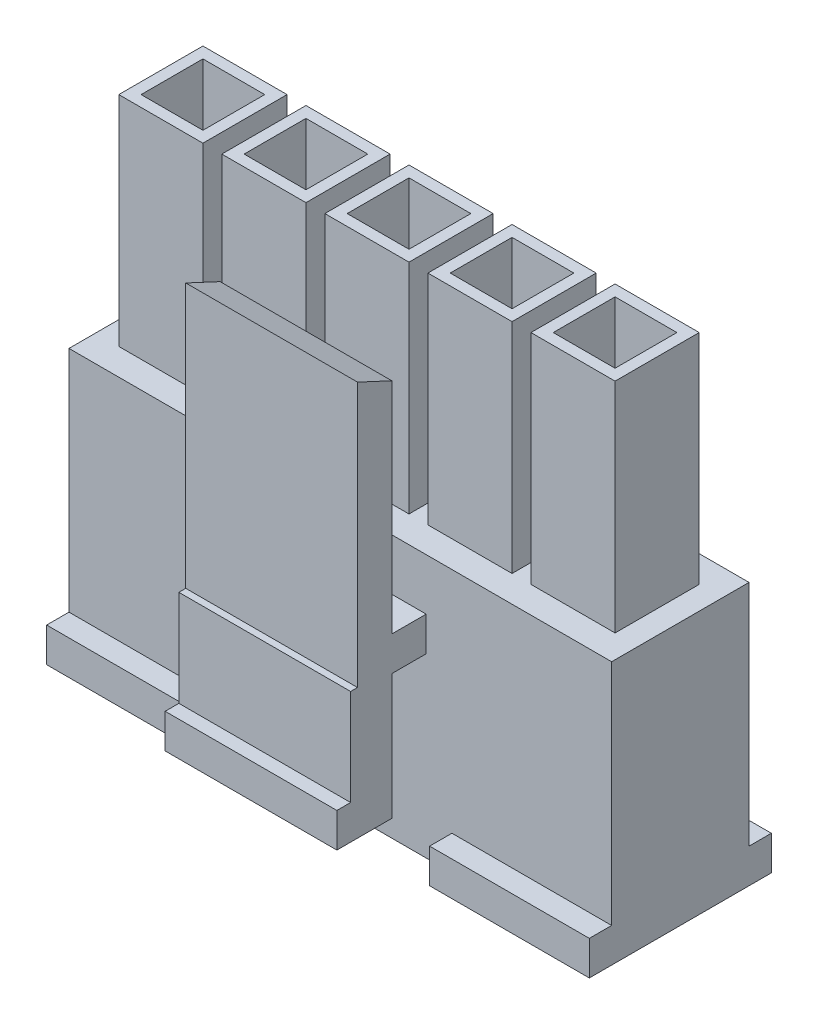
SolidWorks part; units mm, degrees
ref_plane "Front Plane" through (0, 0, 0) normal (0, 0, 1) x (1, 0, 0)
ref_plane "Top Plane" through (0, 0, 0) normal (0, 1, 0) x (1, 0, 0)
ref_plane "Right Plane" through (0, 0, 0) normal (1, 0, 0) x (0, 0, -1)
sketch "Sketch1" plane through (0, 0, 0) normal (0, 1, 0) x (1, 0, 0)
  line L0 (0, 2) -> (0, -2) construction
  line L1 (-7.9, 2) -> (7.9, 2)
  line L2 (-7.9, 2) -> (-7.9, -2)
  line L3 (-7.9, -2) -> (7.9, -2)
  line L4 (7.9, 2) -> (7.9, -2)
  line L5 (-7.9, 2) -> (7.9, -2) construction
  line L6 (-7.9, -2) -> (7.9, 2) construction
  line L7 (-1.35, 1.35) -> (1.35, 1.35)
  line L8 (-1.35, 1.35) -> (-1.35, -1.35)
  line L9 (-1.35, -1.35) -> (1.35, -1.35)
  line L10 (1.35, 1.35) -> (1.35, -1.35)
  line L11 (-1.35, 1.35) -> (1.35, -1.35) construction
  line L12 (-1.35, -1.35) -> (1.35, 1.35) construction
  line L13 (1.65, -1.35) -> (4.35, -1.35)
  line L14 (4.35, 1.35) -> (4.35, -1.35)
  line L15 (1.65, 1.35) -> (4.35, 1.35)
  line L16 (1.65, 1.35) -> (1.65, -1.35)
  line L17 (4.65, -1.35) -> (7.35, -1.35)
  line L18 (7.35, 1.35) -> (7.35, -1.35)
  line L19 (4.65, 1.35) -> (7.35, 1.35)
  line L20 (4.65, 1.35) -> (4.65, -1.35)
  line L21 (-4.65, 1.35) -> (-4.65, -1.35)
  line L22 (-4.65, -1.35) -> (-7.35, -1.35)
  line L23 (-7.35, 1.35) -> (-7.35, -1.35)
  line L24 (-4.65, 1.35) -> (-7.35, 1.35)
  line L25 (-1.65, 1.35) -> (-1.65, -1.35)
  line L26 (-1.65, -1.35) -> (-4.35, -1.35)
  line L27 (-4.35, 1.35) -> (-4.35, -1.35)
  line L28 (-1.65, 1.35) -> (-4.35, 1.35)
  point P0 (0, 0)
  point P6 (0, 0)
  dimension "D1" = 15.8
  dimension "D2" = 4
  dimension "D3" = 2.7
  dimension "D5" = 3
  dimension "D4" = 3
extrude "Boss-Extrude1" add sketch "Sketch1" along normal blind 7.65
sketch "Sketch2" plane through (0, 7.65, 0) normal (0, 1, 0) x (1, 0, 0)
  line L0 (-7.35, 1.35) -> (-4.65, -1.35) construction
  line L1 (-4.35, 1.35) -> (-1.65, -1.35) construction
  line L2 (-1.35, 1.35) -> (1.35, -1.35) construction
  line L3 (1.65, 1.35) -> (4.35, -1.35) construction
  line L4 (4.65, 1.35) -> (7.35, -1.35) construction
  line L6 (-5.1, 0.9) -> (-6.9, 0.9)
  line L7 (-5.1, 0.9) -> (-5.1, -0.9)
  line L8 (-5.1, -0.9) -> (-6.9, -0.9)
  line L9 (-6.9, 0.9) -> (-6.9, -0.9)
  line L10 (-5.1, 0.9) -> (-6.9, -0.9) construction
  line L11 (-5.1, -0.9) -> (-6.9, 0.9) construction
  line L12 (-3.9, -0.9) -> (-2.1, -0.9)
  line L13 (-3.9, -0.9) -> (-3.9, 0.9)
  line L14 (-3.9, 0.9) -> (-2.1, 0.9)
  line L15 (-2.1, -0.9) -> (-2.1, 0.9)
  line L16 (-3.9, -0.9) -> (-2.1, 0.9) construction
  line L17 (-3.9, 0.9) -> (-2.1, -0.9) construction
  line L18 (-0.9, -0.9) -> (0.9, -0.9)
  line L19 (-0.9, -0.9) -> (-0.9, 0.9)
  line L20 (-0.9, 0.9) -> (0.9, 0.9)
  line L21 (0.9, -0.9) -> (0.9, 0.9)
  line L22 (-0.9, -0.9) -> (0.9, 0.9) construction
  line L23 (-0.9, 0.9) -> (0.9, -0.9) construction
  line L24 (2.1, -0.9) -> (3.9, -0.9)
  line L25 (2.1, -0.9) -> (2.1, 0.9)
  line L26 (2.1, 0.9) -> (3.9, 0.9)
  line L27 (3.9, -0.9) -> (3.9, 0.9)
  line L28 (2.1, -0.9) -> (3.9, 0.9) construction
  line L29 (2.1, 0.9) -> (3.9, -0.9) construction
  line L30 (5.1, -0.9) -> (6.9, -0.9)
  line L31 (5.1, -0.9) -> (5.1, 0.9)
  line L32 (5.1, 0.9) -> (6.9, 0.9)
  line L33 (6.9, -0.9) -> (6.9, 0.9)
  line L34 (5.1, -0.9) -> (6.9, 0.9) construction
  line L35 (5.1, 0.9) -> (6.9, -0.9) construction
  line L39 (7.9, -2) -> (7.9, 2)
  line L40 (7.9, 2) -> (-7.9, 2)
  line L41 (-7.9, 2) -> (-7.9, -2)
  line L42 (-7.9, -2) -> (7.9, -2)
  line L43 (7.9, -2) -> (7.9, 2)
  line L44 (7.9, 2) -> (-7.9, 2)
  line L45 (-7.9, 2) -> (-7.9, -2)
  line L46 (-7.9, -2) -> (7.9, -2)
  point P20 (-6, 0)
  point P25 (-3, 0)
  point P30 (0, 0)
  point P36 (3, 0)
  point P41 (6, 0)
  dimension "D1" = 1.8
  dimension "D2" = 0
extrude "Boss-Extrude2" add sketch "Sketch2" against normal blind 1
sketch "Sketch3" plane through (0, 7.65, 0) normal (0, 1, 0) x (1, 0, 0)
  line L0 (-6.9, 0.9) -> (-5.1, -0.9) construction
  line L1 (-3.9, 0.9) -> (-2.1, -0.9) construction
  line L2 (-0.9, 0.9) -> (0.9, -0.9) construction
  line L3 (2.1, 0.9) -> (3.9, -0.9) construction
  line L4 (5.1, 0.9) -> (6.9, -0.9) construction
  line L6 (-4.775, 1.225) -> (-7.225, 1.225)
  line L7 (-4.775, 1.225) -> (-4.775, -1.225)
  line L8 (-4.775, -1.225) -> (-7.225, -1.225)
  line L9 (-7.225, 1.225) -> (-7.225, -1.225)
  line L10 (-4.775, 1.225) -> (-7.225, -1.225) construction
  line L11 (-4.775, -1.225) -> (-7.225, 1.225) construction
  line L12 (-4.225, -1.225) -> (-1.775, -1.225)
  line L13 (-4.225, -1.225) -> (-4.225, 1.225)
  line L14 (-4.225, 1.225) -> (-1.775, 1.225)
  line L15 (-1.775, -1.225) -> (-1.775, 1.225)
  line L16 (-4.225, -1.225) -> (-1.775, 1.225) construction
  line L17 (-4.225, 1.225) -> (-1.775, -1.225) construction
  line L18 (-1.225, -1.225) -> (1.225, -1.225)
  line L19 (-1.225, -1.225) -> (-1.225, 1.225)
  line L20 (-1.225, 1.225) -> (1.225, 1.225)
  line L21 (1.225, -1.225) -> (1.225, 1.225)
  line L22 (-1.225, -1.225) -> (1.225, 1.225) construction
  line L23 (-1.225, 1.225) -> (1.225, -1.225) construction
  line L24 (1.775, -1.225) -> (4.225, -1.225)
  line L25 (1.775, -1.225) -> (1.775, 1.225)
  line L26 (1.775, 1.225) -> (4.225, 1.225)
  line L27 (4.225, -1.225) -> (4.225, 1.225)
  line L28 (1.775, -1.225) -> (4.225, 1.225) construction
  line L29 (1.775, 1.225) -> (4.225, -1.225) construction
  line L30 (4.775, -1.225) -> (7.225, -1.225)
  line L31 (4.775, -1.225) -> (4.775, 1.225)
  line L32 (4.775, 1.225) -> (7.225, 1.225)
  line L33 (7.225, -1.225) -> (7.225, 1.225)
  line L34 (4.775, -1.225) -> (7.225, 1.225) construction
  line L35 (4.775, 1.225) -> (7.225, -1.225) construction
  line L44 (6.9, -0.9) -> (6.9, 0.9)
  line L45 (5.1, -0.9) -> (6.9, -0.9)
  line L46 (5.1, 0.9) -> (5.1, -0.9)
  line L47 (6.9, 0.9) -> (5.1, 0.9)
  line L48 (6.9, -0.9) -> (6.9, 0.9)
  line L49 (5.1, -0.9) -> (6.9, -0.9)
  line L50 (5.1, 0.9) -> (5.1, -0.9)
  line L51 (6.9, 0.9) -> (5.1, 0.9)
  line L52 (3.9, -0.9) -> (3.9, 0.9)
  line L53 (2.1, -0.9) -> (3.9, -0.9)
  line L54 (2.1, 0.9) -> (2.1, -0.9)
  line L55 (3.9, 0.9) -> (2.1, 0.9)
  line L56 (3.9, -0.9) -> (3.9, 0.9)
  line L57 (2.1, -0.9) -> (3.9, -0.9)
  line L58 (2.1, 0.9) -> (2.1, -0.9)
  line L59 (3.9, 0.9) -> (2.1, 0.9)
  line L60 (0.9, -0.9) -> (0.9, 0.9)
  line L61 (-0.9, -0.9) -> (0.9, -0.9)
  line L62 (-0.9, 0.9) -> (-0.9, -0.9)
  line L63 (0.9, 0.9) -> (-0.9, 0.9)
  line L64 (0.9, -0.9) -> (0.9, 0.9)
  line L65 (-0.9, -0.9) -> (0.9, -0.9)
  line L66 (-0.9, 0.9) -> (-0.9, -0.9)
  line L67 (0.9, 0.9) -> (-0.9, 0.9)
  line L68 (-2.1, -0.9) -> (-2.1, 0.9)
  line L69 (-3.9, -0.9) -> (-2.1, -0.9)
  line L70 (-3.9, 0.9) -> (-3.9, -0.9)
  line L71 (-2.1, 0.9) -> (-3.9, 0.9)
  line L72 (-2.1, -0.9) -> (-2.1, 0.9)
  line L73 (-3.9, -0.9) -> (-2.1, -0.9)
  line L74 (-3.9, 0.9) -> (-3.9, -0.9)
  line L75 (-2.1, 0.9) -> (-3.9, 0.9)
  line L76 (-6.9, 0.9) -> (-6.9, -0.9)
  line L77 (-5.1, 0.9) -> (-6.9, 0.9)
  line L78 (-5.1, -0.9) -> (-5.1, 0.9)
  line L79 (-6.9, -0.9) -> (-5.1, -0.9)
  line L80 (-6.9, 0.9) -> (-6.9, -0.9)
  line L81 (-5.1, 0.9) -> (-6.9, 0.9)
  line L82 (-5.1, -0.9) -> (-5.1, 0.9)
  line L83 (-6.9, -0.9) -> (-5.1, -0.9)
  point P20 (-6, 0)
  point P25 (-3, 0)
  point P30 (0, 0)
  point P36 (3, 0)
  point P41 (6, 0)
  dimension "D1" = 2.45
  dimension "D2" = 0
  dimension "D3" = 0
  dimension "D4" = 0
  dimension "D5" = 0
  dimension "D6" = 0
extrude "Boss-Extrude3" add sketch "Sketch3" along normal offset from surface (6.35 mm away) 14 up to face at (6, 0, 0)
sketch "Sketch4" plane through (0, 0, 0) normal (0, -1, 0) x (1, 0, 0)
  line L0 (-7.9, -2) -> (-7.9, 2) construction
  line L1 (7.9, 2.65) -> (-7.9, 2.65)
  line L2 (7.9, 2.65) -> (7.9, -2.65)
  line L3 (7.9, -2.65) -> (-7.9, -2.65)
  line L4 (-7.9, 2.65) -> (-7.9, -2.65)
  line L5 (7.9, 2.65) -> (-7.9, -2.65) construction
  line L6 (7.9, -2.65) -> (-7.9, 2.65) construction
  line L7 (0, 3.4297) -> (0, -4.5863) construction
  line L8 (-7.9, 2) -> (7.9, 2) construction
  line L9 (-3.25, 2.65) -> (3.25, 2.65)
  line L10 (-3.25, 2.65) -> (-3.25, 2)
  line L11 (-3.25, 2) -> (3.25, 2)
  line L12 (3.25, 2.65) -> (3.25, 2)
  line L13 (-3.25, 2.65) -> (3.25, 2) construction
  line L14 (-3.25, 2) -> (3.25, 2.65) construction
  point P0 (0, 0)
  point P9 (0, 2.325)
  line M19 (7.9, 2) -> (-7.9, 2)
  line M21 (-7.9, -2) -> (7.9, -2)
  dimension "D1" = 5.3
  dimension "D2" = 6.5
extrude "Boss-Extrude4" add sketch "Sketch4" against normal blind 1 contours L10 L1 L4 M19 | L1 L12 L2 M19 | L4 L3 L2 M21
sketch "Sketch5" plane through (0, 0, 0) normal (1, 0, 0) x (0, 0, -1)
  line L0 (-3.7698, 5.65) -> (4.8186, 5.65) construction
  line L1 (-2, 7.65) -> (2, 7.65) construction
  line L2 (-2, 7.65) -> (-2, 1) construction
  line L3 (-3, 6.15) -> (-2, 6.15)
  line L4 (-3, 6.15) -> (-3, 5.15)
  line L5 (-3, 5.15) -> (-2, 5.15)
  line L6 (-2, 6.15) -> (-2, 5.15)
  line L7 (-3, 6.15) -> (-2, 5.15) construction
  line L8 (-3, 5.15) -> (-2, 6.15) construction
  line L9 (-1.225, 14) -> (1.225, 14) construction
  line L10 (-4, 13) -> (-3, 13)
  line L11 (-4, 13) -> (-4, 1.5)
  line L12 (-4, 1.5) -> (-3, 1.5)
  line L13 (-3, 13) -> (-3, 1.5)
  line L14 (-2.65, 0) -> (2.65, 0) construction
  line L15 (-4, 13) -> (-3, 12.5337)
  line L17 (-4, 5.3) -> (-4.2, 5.3)
  line L18 (-4, 5.3) -> (-4, 1.5)
  line L19 (-4, 1.5) -> (-4.2, 1.5)
  line L20 (-4.2, 5.3) -> (-4.2, 1.5)
  line L21 (-4.2, 2.5) -> (-4.6, 2.5)
  line L22 (-4.2, 2.5) -> (-4.2, 1.5)
  line L23 (-4.2, 1.5) -> (-4.6, 1.5)
  line L24 (-4.6, 2.5) -> (-4.6, 1.5)
  point P4 (-2.5, 5.65)
  dimension "D1" = 2
  dimension "D2" = 1
  dimension "D3" = 1
  dimension "D4" = 1.5
  dimension "D5" = 25
  dimension "D6" = 0.2
  dimension "D7" = 0.4
  dimension "D8" = 1
  dimension "D9" = 3.8
extrude "Boss-Extrude5" add sketch "Sketch5" along normal mid plane 5 contours L15 L11 L12 L13 L4 | L6 L3 L4 L5 | L17 L20 L19 L11 | L21 L24 L23 L20
